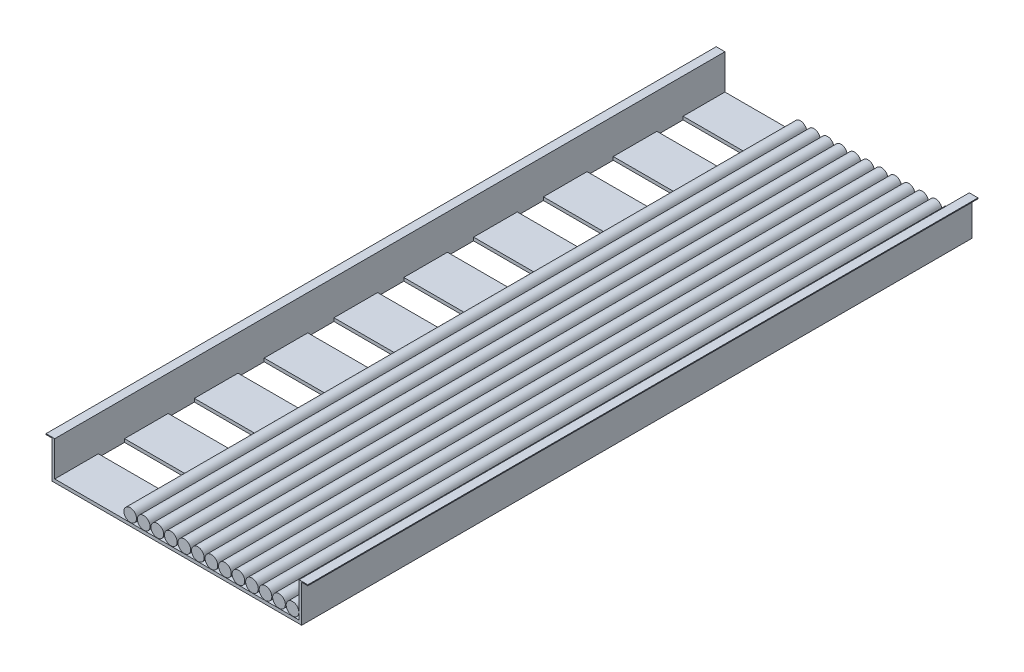
SolidWorks part; units mm, degrees
ref_plane "Alzado" through (0, 0, 0) normal (0, 0, 1) x (1, 0, 0)
ref_plane "Planta" through (0, 0, 0) normal (0, 1, 0) x (1, 0, 0)
ref_plane "Vista lateral" through (0, 0, 0) normal (1, 0, 0) x (0, 0, -1)
sketch "Croquis1" plane through (0, 0, 0) normal (0, 0, 1) x (1, 0, 0)
  line L1 (-300, -60) -> (300, -60)
  line L2 (-300, -60) -> (-300, 60)
  line L3 (-300, 60) -> (300, 60)
  line L4 (300, -60) -> (300, 60)
  line L5 (-300, -60) -> (300, 60) construction
  line L6 (-300, 60) -> (300, -60) construction
  point P0 (0, 0)
  dimension "D1" = 120
  dimension "D2" = 600
extrude "Saliente-Extruir1" add sketch "Croquis1" along normal blind 4840
sketch "Croquis2" plane through (0, 0, 4840) normal (0, 0, 1) x (1, 0, 0)
  line L0 (-280, -20) -> (-280, 60)
  line L2 (-280, -20) -> (280, -20)
  line L3 (300, 60) -> (-300, 60) construction
  line L5 (-280, 60) -> (280, 60)
  line L6 (280, 60) -> (280, -20)
  line L7 (-300, 60) -> (-300, -60) construction
  line L8 (300, -60) -> (300, 60) construction
  line L9 (-300, -60) -> (300, -60) construction
  dimension "D1" = 20
  dimension "D2" = 20
  dimension "D3" = 40
extrude "Cortar-Extruir1" cut sketch "Croquis2" against normal up to surface (4840 mm away) up to face at (0, 0, 0)
sketch "Croquis3" plane through (0, 0, 4840) normal (0, 0, 1) x (1, 0, 0)
  line L0 (-300, 58) -> (-286, 58)
  line L1 (-300, 60) -> (-300, -60) construction
  line L2 (-286, 58) -> (-286, -27.4237)
  line L3 (-286, -27.4237) -> (286, -27.4237)
  line L4 (286, -27.4237) -> (286, 58)
  line L5 (286, 58) -> (300, 58)
  line L6 (300, -60) -> (300, 60) construction
  line L7 (300, 58) -> (300, 60)
  line L8 (300, 60) -> (280, 60) construction
  line L9 (280, -20) -> (280, 60) construction
  line L10 (-280, 60) -> (-300, 60) construction
  line L11 (-280, 60) -> (-280, -20) construction
  line L12 (-300, 58) -> (-300, -60)
  line L13 (-300, -60) -> (300, -60)
  line L14 (300, -60) -> (300, 58)
  point P20 (-280, 20)
  line M10 (-300, 60) -> (-300, -60)
  line M11 (-300, -60) -> (300, -60)
  line M12 (300, -60) -> (300, 60)
  dimension "D1" = 2
  dimension "D2" = 6
  dimension "D3" = 2
  dimension "D4" = 6
extrude "Cortar-Extruir2" cut sketch "Croquis3" against normal up to surface (4840 mm away) contours L5 L4 L3 L2 L0 M10 M11 M12 up to face at (0, 10, 0)
sketch "Croquis4" plane through (0, -20, 0) normal (0, 1, 0) x (1, 0, 0)
  line L0 (-280, 0) -> (-280, -4840) construction
  line L1 (280, -4740) -> (-280, -4740)
  line L2 (280, -4740) -> (280, -4680)
  line L3 (280, -4680) -> (-280, -4680)
  line L4 (-280, -4740) -> (-280, -4680)
  line L5 (280, -4740) -> (-280, -4680) construction
  line L6 (280, -4680) -> (-280, -4740) construction
  line L7 (-280, -4840) -> (280, -4840) construction
  point P0 (0, -4710)
  dimension "D1" = 100
  dimension "D2" = 60
extrude "Cortar-Extruir3" cut sketch "Croquis4" against normal blind 4000
pattern_linear "MatrizL1" count 30 spacing 160 along (0, 0, -1) of "Cortar-Extruir3"
sketch "Croquis5" plane through (0, 0, 0) normal (0, 0, -1) x (-1, 0, 0)
  line L0 (-280, -20) -> (-280, 60) construction
  line L1 (280, -20) -> (-280, -20) construction
  circle A0 centre (-265, -5) radius 14.5
  dimension "D1" = 29
  dimension "D2" = 15
  dimension "D3" = 15
extrude "Saliente-Extruir2" add sketch "Croquis5" against normal up to surface (4840 mm away) separate body up to face at (0, 31.4294, 4840)
pattern_linear "MatrizL2" count 13 spacing 31 along (-1, 0, 0) of "Saliente-Extruir2"
sketch "Croquis6" plane through (0, 0, 0) normal (0, 0, -1) x (-1, 0, 0)
  line L0 (-300, 60) -> (300, 60)
  line L1 (300, 60) -> (300, -29.7242)
  line L2 (300, -29.7242) -> (-300, -29.7242)
  line L3 (-300, -29.7242) -> (-300, 60)
extrude "Cortar-Extruir4" cut sketch "Croquis6" against normal blind 3304
